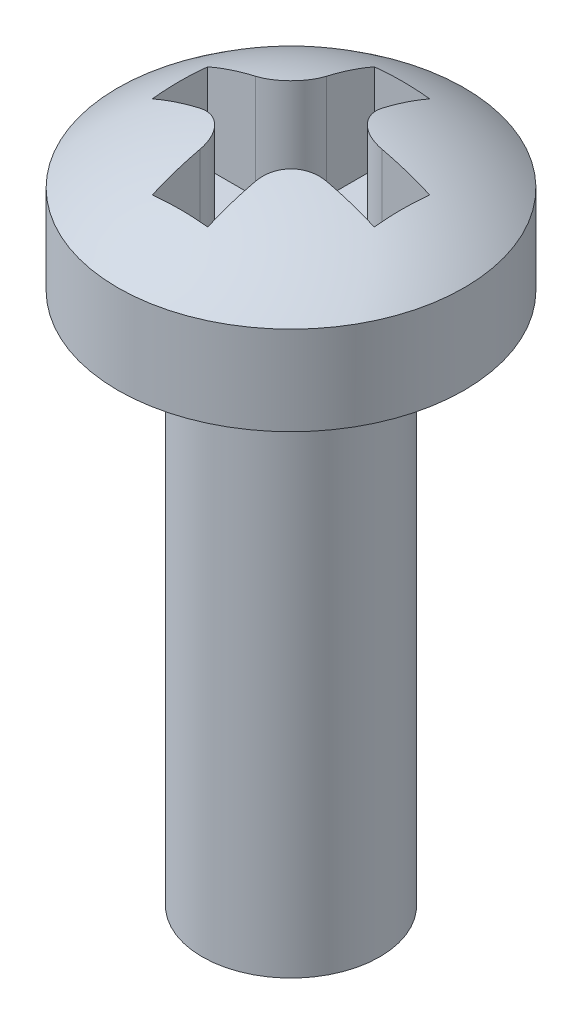
SolidWorks part; units mm, degrees
ref_plane "Front Plane" through (0, 0, 0) normal (0, 0, 1) x (1, 0, 0)
ref_plane "Top Plane" through (0, 0, 0) normal (0, 1, 0) x (1, 0, 0)
ref_plane "Right Plane" through (0, 0, 0) normal (1, 0, 0) x (0, 0, -1)
sketch "Sketch1" plane through (0, 0, 0) normal (0, 1, 0) x (1, 0, 0)
  circle A0 centre (0, 0) radius 2
  dimension "D1" = 4
extrude "Boss-Extrude1" add sketch "Sketch1" along normal blind 12
thread "Thread1" pitch 0.7 start angle 0, offset 0, length 12, pitch 0.7, diameter 4
ref_plane "Plane1" through (-2, 12, 0) normal (0, 0, 1) x (-1, 0, 0)
sketch "Thread Profile1" plane through (-2, 12, 0) normal (0, 0, 1) x (-1, 0, 0)
  line L0 (0, 0) -> (0, 0.7) construction
  line L11 (0, 0) -> (0, 0.6125)
  line L12 (0, 0.6125) -> (-0.3789, 0.3937)
  line L13 (-0.3789, 0.3937) -> (-0.3789, 0.2187)
  line L15 (-0.3789, 0.2187) -> (0, 0)
  line L17 (-0.3789, 0.3062) -> (0, 0.3062) construction
  point P2 (0, 0)
  dimension "Pitch" = 0.7
  dimension "Profile_Angle" = 60
  dimension "Profile_Land" = 0.175
  dimension "Profile_Height" = 0.3789
sketch "Sketch5" plane through (0, 12, 0) normal (0, 1, 0) x (1, 0, 0)
  circle A0 centre (0, 0) radius 3.9
  dimension "D1" = 7.8
extrude "Boss-Extrude2" add sketch "Sketch5" along normal blind 2
sketch "Sketch6" plane through (0, 0, 0) normal (1, 0, 0) x (0, 0, -1)
  line L0 (3.9, 14) -> (-3.9, 14) construction
  line L1 (0, 15.346) -> (0, 14)
  line L2 (3.9, 14) -> (0, 14)
  arc A0 (3.9, 14) -> (0, 15.346) centre (0, 9.0227) ccw
  point P3 (2.0629, 15)
  dimension "D1" = 1
revolve "Revolve1" add sketch "Sketch6" angle 360 about L1
ref_plane "Plane2" through (0, 15.346, 0) normal (0, 1, 0) x (1, 0, 0)
sketch "Sketch7" plane through (0, 15.346, 0) normal (0, 1, 0) x (1, 0, 0)
  line L0 (-2.5, 0) -> (2.5, 0) construction
  line L1 (0, 2.5) -> (0, -2.5) construction
  line L2 (-2.5, -0.625) -> (-1.425, -0.625)
  line L3 (-0.625, 2.5) -> (-0.625, 1.425)
  line L4 (-2.5, 0.625) -> (-1.425, 0.625)
  line L5 (0.625, 2.5) -> (0.625, 1.425)
  line L6 (2.5, 0.625) -> (2.5, -0.625)
  line L7 (0.625, -2.5) -> (-0.625, -2.5)
  line L8 (-2.5, 0.625) -> (-2.5, -0.625)
  line L9 (0.625, 2.5) -> (-0.625, 2.5)
  line L10 (1.425, 0.625) -> (2.5, 0.625)
  line L11 (-2.5, 0.625) -> (2.5, 0.625) construction
  line L12 (0.625, -1.425) -> (0.625, -2.5)
  line L13 (0.625, 2.5) -> (0.625, -2.5) construction
  line L14 (1.425, -0.625) -> (2.5, -0.625)
  line L15 (-2.5, -0.625) -> (2.5, -0.625) construction
  line L16 (-0.625, -1.425) -> (-0.625, -2.5)
  line L17 (-0.625, 2.5) -> (-0.625, -2.5) construction
  arc A0 (-1.425, 0.625) -> (-0.625, 1.425) centre (-1.425, 1.425) ccw
  arc A1 (-1.425, -0.625) -> (-0.625, -1.425) centre (-1.425, -1.425) cw
  arc A2 (0.625, -1.425) -> (1.425, -0.625) centre (1.425, -1.425) cw
  arc A3 (1.425, 0.625) -> (0.625, 1.425) centre (1.425, 1.425) cw
  point P4 (0, 0)
  point P8 (0, 0)
  point P24 (-0.625, -0.625)
  point P27 (0.625, -0.625)
  dimension "D4" = 0.8
  dimension "D1" = 5
  dimension "D2" = 0.625
  dimension "D3" = 0.625
extrude "Cut-Extrude1" cut sketch "Sketch7" against normal offset from surface (2.546 mm away) 0.8 up to face at (0, 12, 2)
